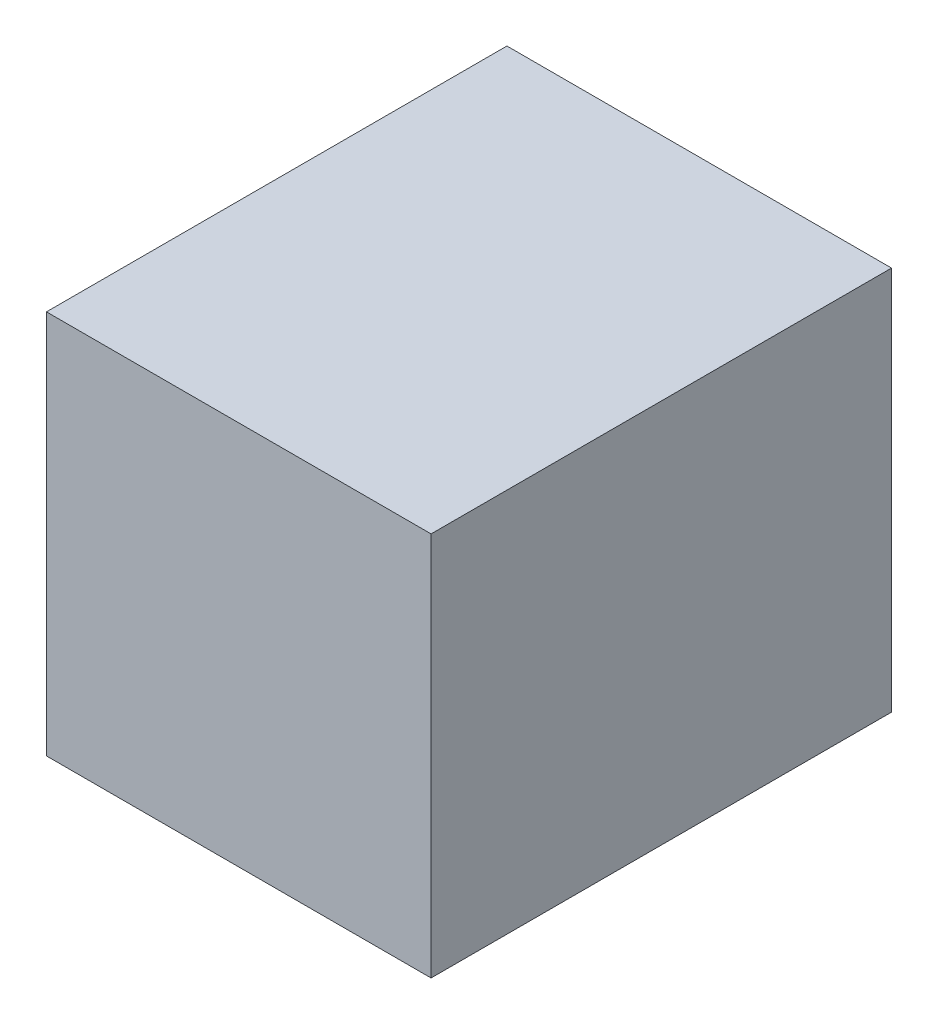
SolidWorks part; units mm, degrees
ref_plane "Piano frontale" through (0, 0, 0) normal (0, 0, 1) x (1, 0, 0)
ref_plane "Piano superiore" through (0, 0, 0) normal (0, 1, 0) x (1, 0, 0)
ref_plane "Piano destro" through (0, 0, 0) normal (1, 0, 0) x (0, 0, -1)
sketch "Schizzo1" plane through (0, 0, 0) normal (0, 0, 1) x (1, 0, 0)
  line L1 (66.8216, 66.8216) -> (-66.8216, 66.8216)
  line L2 (-66.8216, 66.8216) -> (-66.8216, -66.8216)
  line L3 (-66.8216, -66.8216) -> (66.8216, -66.8216)
  line L4 (66.8216, -66.8216) -> (66.8216, 66.8216)
  circle A0 centre (0, 0) radius 66.8216 construction
  dimension "D1" = 94.5
extrude "Estrusione-Estrusione1" add sketch "Schizzo1" along normal blind 160
